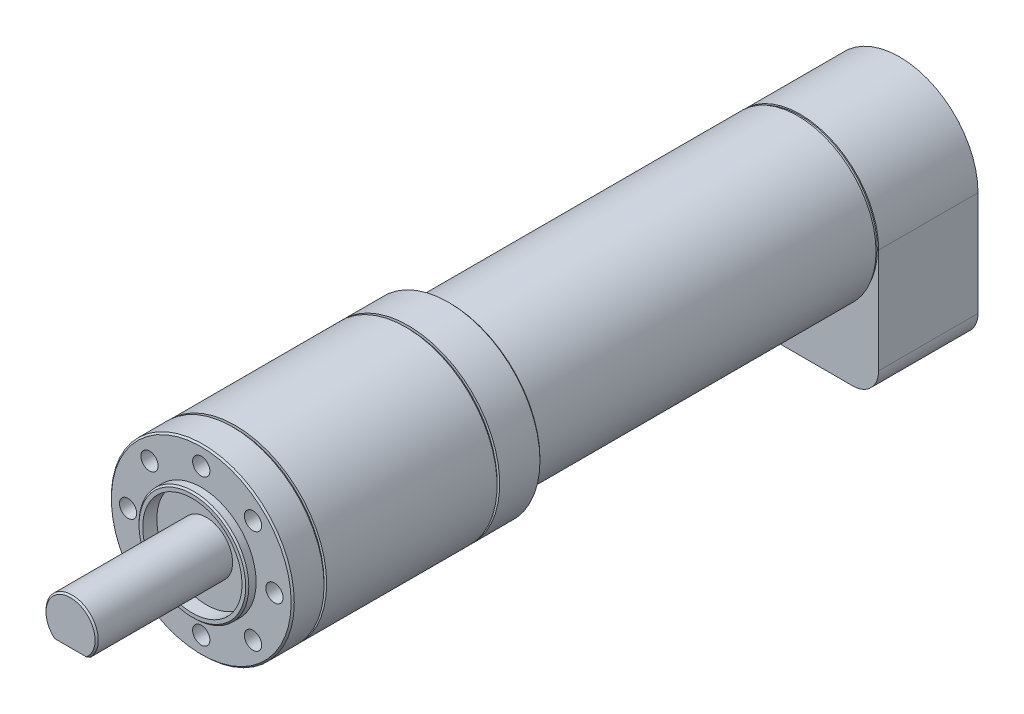
SolidWorks part; units mm, degrees
ref_plane "前视基准面" through (0, 0, 0) normal (0, 0, 1) x (1, 0, 0)
ref_plane "上视基准面" through (0, 0, 0) normal (0, 1, 0) x (1, 0, 0)
ref_plane "右视基准面" through (0, 0, 0) normal (1, 0, 0) x (0, 0, -1)
sketch "草图1" plane through (0, 0, 0) normal (0, 0, 1) x (1, 0, 0)
  circle A0 centre (0, 0) radius 17.5
  dimension "D1" = 35
extrude "凸台-拉伸1" add sketch "草图1" along normal blind 47.6
sketch "草图2" plane through (0, 0, 47.6) normal (0, 0, 1) x (1, 0, 0)
  circle A0 centre (0, 0) radius 9.5
  dimension "D1" = 19
extrude "切除-拉伸1" cut sketch "草图2" against normal blind 1
sketch "草图3" plane through (0, 0, 47.6) normal (0, 0, 1) x (1, 0, 0)
  circle A0 centre (0, 0) radius 9.5
  circle A1 centre (0, 0) radius 10.5
  dimension "D1" = 21
extrude "凸台-拉伸2" add sketch "草图3" along normal blind 1.7
sketch "草图4" plane through (0, 0, 46.6) normal (0, 0, 1) x (1, 0, 0)
  circle A0 centre (0, 0) radius 5
  dimension "D1" = 10
extrude "凸台-拉伸3" add sketch "草图4" along normal blind 26
sketch "草图5" plane through (0, 0, 72.6) normal (0, 0, 1) x (1, 0, 0)
  line L0 (-3.4699, -3.6) -> (3.4699, -3.6)
  circle A0 centre (0, 0) radius 5 construction
  arc A1 (-3.4699, -3.6) -> (3.4699, -3.6) centre (0, 0) ccw
  dimension "D1" = 3.6
extrude "切除-拉伸2" cut sketch "草图5" against normal blind 20
sketch "草图11" plane through (0, 0, 47.6) normal (0, 0, 1) x (1, 0, 0)
  circle A0 centre (0, 0) radius 14 construction
  circle A1 centre (0, 14) radius 1.5
  circle A2 centre (9.8995, 9.8995) radius 1.5
  circle A3 centre (14, 0) radius 1.5
  circle A4 centre (9.8995, -9.8995) radius 1.5
  circle A5 centre (0, -14) radius 1.5
  circle A6 centre (-9.8995, -9.8995) radius 1.5
  circle A7 centre (-14, 0) radius 1.5
  circle A8 centre (-9.8995, 9.8995) radius 1.5
  point P22 (0, 0)
  dimension "D1" = 28
  dimension "D2" = 3
  dimension "D3" = 8
sketch "草图12" plane through (0, 0, 0) normal (0, 0, -1) x (-1, 0, 0)
  circle A0 centre (0, 0) radius 15
  dimension "D1" = 30
extrude "凸台-拉伸4" add sketch "草图12" along normal blind 67
sketch "草图15" plane through (0, 0, -67) normal (0, 0, -1) x (-1, 0, 0)
  line L3 (-15, 0) -> (-15, -25)
  line L4 (-15, -25) -> (15, -25)
  line L5 (15, 0) -> (15, -25)
  circle A0 centre (0, 0) radius 15 construction
  circle A1 centre (0, 0) radius 15 construction
  arc A2 (-15, 0) -> (15, 0) centre (0, 0) cw
  dimension "D1" = 25
extrude "凸台-拉伸5" add sketch "草图15" along normal blind 19
hole_wizard "M4 螺纹孔6" positions "3D草图8" profile "草图17" tap size "M4" standard "GB"
sketch3d "3D草图8"
  point P0 (0, 14, 47.6)
  point P3 (-9.8995, 9.8995, 47.6)
  point P6 (-14, 0, 47.6)
  point P9 (-9.8995, -9.8995, 47.6)
  point P12 (0, -14, 47.6)
  point P15 (9.8995, -9.8995, 47.6)
  point P18 (14, 0, 47.6)
  point P21 (9.8995, 9.8995, 47.6)
sketch "草图17" plane through (0, 14, 47.6) normal (1, 0, 0) x (0, -1, 0)
  line L0 (0, 0) -> (0, 8.9914)
  line L1 (0, 8.9914) -> (1.65, 8)
  line L2 (1.65, 8) -> (1.65, 0)
  line L5 (1.65, 0) -> (0, 0)
  line L10 (0, 8.9914) -> (-1.65, 8) construction
  line L11 (0, -6.35) -> (0, 107.95) construction
  dimension "螺纹孔钻头直径" = 3.3
  dimension "螺纹孔钻头深度" = 8
  dimension "导头角度" = 118
cosmetic thread "孔螺蚊线26" parameters "D1"=8, "D2"=4
cosmetic thread "孔螺蚊线27" parameters "D1"=8, "D2"=4
cosmetic thread "孔螺蚊线28" parameters "D1"=8, "D2"=4
cosmetic thread "孔螺蚊线29" parameters "D1"=8, "D2"=4
cosmetic thread "孔螺蚊线30" parameters "D1"=8, "D2"=4
cosmetic thread "孔螺蚊线31" parameters "D1"=8, "D2"=4
cosmetic thread "孔螺蚊线32" parameters "D1"=8, "D2"=4
cosmetic thread "孔螺蚊线33" parameters "D1"=8, "D2"=4
ref_plane "基准面1" through (0, 0, 41.6) normal (0, 0, 1) x (1, 0, 0)
sketch "草图18" plane through (0, 0, 41.6) normal (0, 0, 1) x (1, 0, 0)
  circle A0 centre (0, 0) radius 17.5
  circle A1 centre (0, 0) radius 17
  circle A2 centre (0, 0) radius 17.5 construction
  dimension "D1" = 0.5
extrude "切除-拉伸5" cut sketch "草图18" against normal blind 0.5
ref_plane "基准面2" through (0, 0, 8) normal (0, 0, -1) x (-1, 0, 0)
sketch "草图19" plane through (0, 0, 8) normal (0, 0, -1) x (-1, 0, 0)
  circle A0 centre (0, 0) radius 17.5
  circle A1 centre (0, 0) radius 17
  circle A2 centre (0, 0) radius 17.5 construction
  dimension "D1" = 0.5
extrude "切除-拉伸6" cut sketch "草图19" against normal blind 0.5
sketch "草图20" plane through (0, 0, -67) normal (0, 0, 1) x (1, 0, 0)
  circle A0 centre (0, 0) radius 15
  circle A1 centre (0, 0) radius 14.75
  dimension "D1" = 30
  dimension "D2" = 29.5
extrude "切除-拉伸7" cut sketch "草图20" along normal blind 0.5
chamfer "倒角1" distance 0.3 angle 45 1 edges at (0, 5, 72.6)
chamfer "倒角2" distance 0.3 angle 45 1 edges at (10.5, 0, 49.3)
fillet "圆角1" radius 5 2 edges at (15, -25, -76.5) (-15, -25, -76.5)
